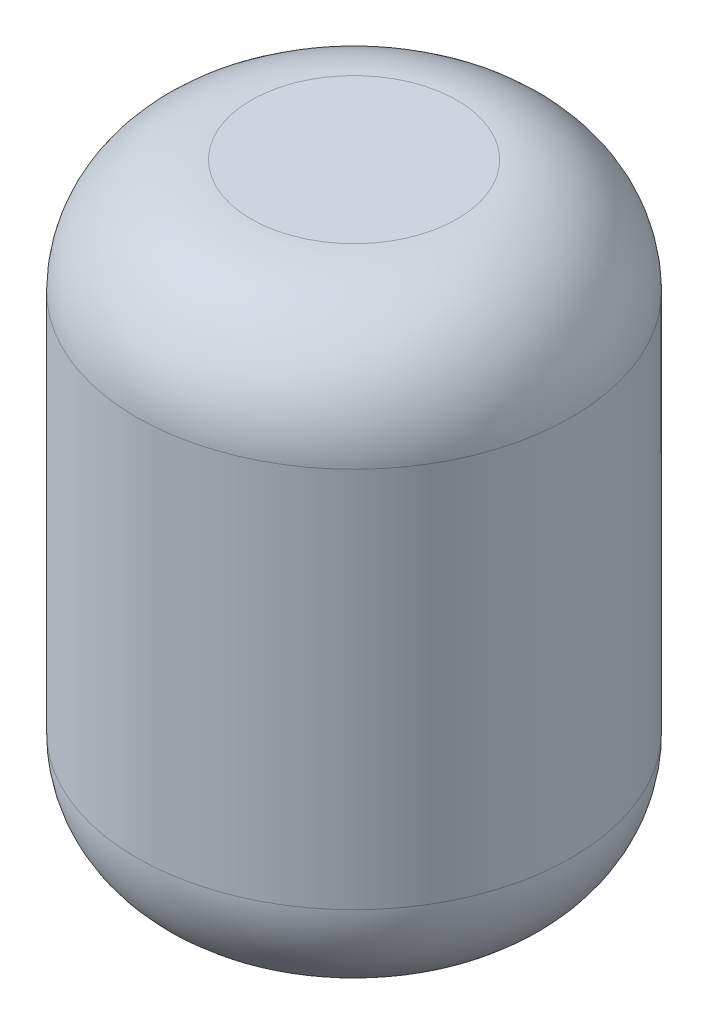
SolidWorks part; units mm, degrees
ref_plane "Front Plane" through (0, 0, 0) normal (0, 0, 1) x (1, 0, 0)
ref_plane "Top Plane" through (0, 0, 0) normal (0, 1, 0) x (1, 0, 0)
ref_plane "Right Plane" through (0, 0, 0) normal (1, 0, 0) x (0, 0, -1)
sketch "Sketch1" plane through (0, 0, 0) normal (0, 1, 0) x (1, 0, 0)
  circle A0 centre (0, 0) radius 72.3885
extrude "Boss-Extrude1" add sketch "Sketch1" along normal blind 203.2
fillet "Fillet1" radius 38.1 2 edges at (0, 0, 72.3885) (0, 203.2, 72.3885)
